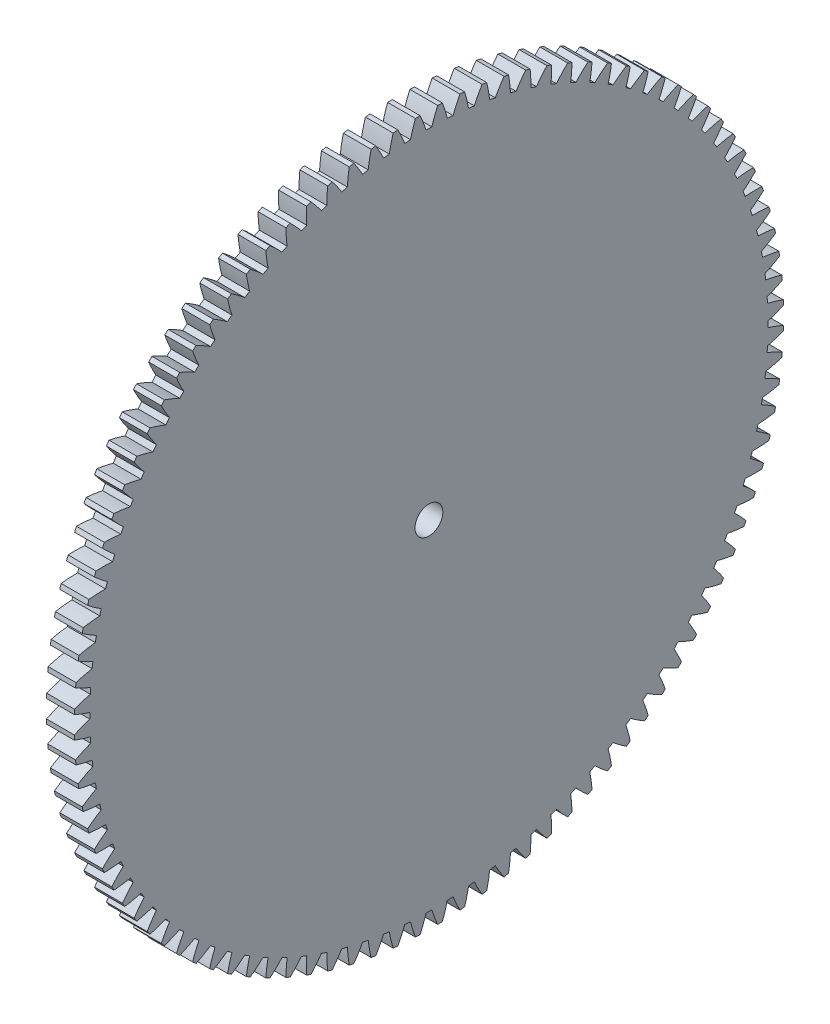
SolidWorks part; units mm, degrees
ref_plane "Plane1" through (0, 0, 0) normal (0, 0, 1) x (1, 0, 0)
ref_plane "Plane2" through (0, 0, 0) normal (0, 1, 0) x (1, 0, 0)
ref_plane "Plane3" through (0, 0, 0) normal (1, 0, 0) x (0, 0, -1)
sketch "HoldingSke" plane through (0, 0, 0) normal (0, 1, 0) x (1, 0, 0)
  line L0 (0, 0) -> (-0.1736, -0.9848)
  line L1 (-15, 0) -> (100, 0) construction
  line L2 (0, 0) -> (-2.1039, 2.3779)
  line L3 (0, 0) -> (-11.863, 4.5341)
  line L4 (0, 0) -> (-1.4996, 8.5048)
  line L5 (0, 0) -> (-46.8476, -17.4728)
  line L6 (0, 0) -> (-3.3159, -2.2372)
  line L7 (-2.1039, 2.3779) -> (8.6586, 51.2059)
  line L8 (-76.2, 54.61) -> (-75.5, 54.61)
  line L9 (-71.009, 38.7566) -> (-53.1078, 45.2721)
  line L10 (-76.2, 71.12) -> (104.1128, 71.12)
  line L11 (0, 0) -> (-4, 0)
  line L12 (-76.2, 101.6) -> (-76.162, 101.6)
  line L13 (24.9733, 27.94) -> (52.9518, 28.4284)
  line L14 (24.9733, 27.94) -> (24.9743, 27.94)
  line L15 (24.9733, 27.94) -> (100.4006, 29.5858)
  line L16 (-63.627, -1) -> (-12.827, -1)
  circle A0 centre (0, 0) radius 2
  circle A1 centre (0, 0) radius 37.5
  circle A2 centre (0, 0) radius 37.5
  circle A3 centre (0, 0) radius 2
  dimension "Hub_dia" = 75
  dimension "Num_teeth" = 100
  dimension "Pitch" = 1
  dimension "Overall_len" = 50
  dimension "Show_teeth" = 100
  dimension "Thickness" = 4
  dimension "OAL" = 50.0001
  dimension "Ap" = 20
  dimension "H" = 19.05
  dimension "Pitch_radius" = 180.3128
  dimension "Width" = 4
  dimension "Backlash" = 0.038
  dimension "Addendum_fac" = 1
  dimension "Dedendum_fac" = 1.25
  dimension "Clearance_fac" = 0.25
  dimension "Dedendum_add" = 0.001
  dimension "Module" = 1
sketch "BasProSke" plane through (0, 0, 0) normal (0, 1, 0) x (1, 0, 0)
  line L0 (-10, 0) -> (60, 0) construction
  line L1 (0, 0) -> (0, 51)
  line L2 (0, 0) -> (4, 0)
  line L3 (4, 0) -> (4, 51)
  line L4 (4, 51) -> (0, 51)
  dimension "Thickness" = 4
revolve "Base-Revolve" add sketch "BasProSke" angle 360 about L0
sketch "TooCutSke" plane through (0, 0, 0) normal (1, 0, 0) x (0, 0, -1)
  line L1 (0, 0) -> (0, 107) construction
  line L2 (0, 0) -> (-0.8519, 49.9927) construction
  line L3 (0, 0) -> (-3.1408, 99.9403) construction
  line L4 (-0.8519, 49.9927) -> (-1.5704, 49.9702) construction
  arc A0 (0.4147, 48.7472) -> (-0.4147, 48.7472) centre (0, 0) ccw
  arc A1 (1.2795, 51.0094) -> (-1.2795, 51.0094) centre (0, 0) ccw
  circle A2 centre (0, 0) radius 50 construction
  circle A3 centre (0, 0) radius 46.9846 construction
  arc A4 (-0.4147, 48.7472) -> (-1.2795, 51.0094) centre (-19.4942, 42.7496) ccw
  arc A5 (1.2795, 51.0094) -> (0.4147, 48.7472) centre (19.4942, 42.7496) ccw
  dimension "Pitch_dia" = 100
  dimension "Base_dia" = 93.9693
  dimension "Flank_rad" = 20
extrude "ToothCut" cut sketch "TooCutSke" along normal through all
fillet "Breaks" [suppressed] radius 0.02
fillet "RootFillets" [suppressed] radius 0.251
pattern_circular "TeethCuts" count 100 every 3.6 about axis through (-10, 0, 0) along (1, 0, 0) of "ToothCut", "RootFillets", "Breaks"
sketch "HubNeaOneSke" plane through (0, 0, 0) normal (-1, 0, 0) x (0, 0, 1)
  circle A0 centre (0, 0) radius 37.5
extrude "HubNearOne" [suppressed] add sketch "HubNeaOneSke" along normal blind 46.0001
sketch "HubNeaBotSke" plane through (0, 0, 0) normal (-1, 0, 0) x (0, 0, 1)
  circle A0 centre (0, 0) radius 37.5
extrude "HubNearBoth" [suppressed] add sketch "HubNeaBotSke" along normal blind 23
ref_plane "FarPln" through (4, 0, 0) normal (1, 0, 0) x (0, 0, -1)
sketch "HubFarSke" plane through (4, 0, 0) normal (1, 0, 0) x (0, 0, -1)
  circle A0 centre (0, 0) radius 37.5
extrude "HubFar" [suppressed] add sketch "HubFarSke" along normal blind 23
sketch "BorSke" plane through (0, 0, 0) normal (1, 0, 0) x (0, 0, -1)
  circle A0 centre (0, 0) radius 2
extrude "Bore" cut sketch "BorSke" along normal mid plane 100.0001
sketch "KeySke" plane through (0, 0, 0) normal (1, 0, 0) x (0, 0, -1)
  line L0 (-0.8, 0) -> (-0.8, 2.7)
  line L1 (-0.8, 2.7) -> (0.8, 2.7)
  line L2 (0.8, 2.7) -> (0.8, 0)
  line L3 (0, 0) -> (0, 34) construction
  line L4 (-0.8, 0) -> (0.8, 0)
extrude "Keyway" [suppressed] cut sketch "KeySke" along normal mid plane 100.0001
pattern_circular "Keyway2" [suppressed] count 2 every 90 about axis through (-10, 0, 0) along (1, 0, 0)
equation "' \"Module@HoldingSke\" = 6.35"
equation "' \"Num_teeth@HoldingSke\" = 12"
equation "' \"Ap@HoldingSke\" =  20"
equation "' \"Ap@HoldingSke\" = 20"
equation "' \"Width@HoldingSke\" = 0.5 * 25.4"
equation "' \"Hub_dia@HoldingSke\"= 1 * 25.4"
equation "' \"Hub_dia@HoldingSke\" = 1 * 25.4"
equation "' \"Overall_len@HoldingSke\" = 1.0 * 25.4"
equation "' \"Bore@HoldingSke\" = 0.75 * 25.4"
equation "' \"T_dim@HoldingSke\" = 0.1 * 25.4"
equation "' \"Width@KeySke\" = 0.25 * 25.4"
equation "' \"Show_teeth@HoldingSke\" = 13"
equation "' \"Backlash@HoldingSke\" = 0.009 * 25.4"
equation "' \"Addendum_fac@HoldingSke\" = 1.0"
equation "' \"Dedendum_fac@HoldingSke\" = 1.25"
equation "' \"Dedendum_add@HoldingSke\" = 0.00005 * 25.4"
equation "' \"Clearance_fac@HoldingSke\" = 0.25"
equation "\"Pitch@HoldingSke\" = 1 / \"Module@HoldingSke\""
equation "\"Overcut_dia@TooCutSke\" = (\"Num_teeth@HoldingSke\" + 2 * \"Addendum_fac@HoldingSke\") / \"Pitch@HoldingSke\" + 0.002 * 25.4"
equation "\"Pitch_dia@TooCutSke\" = \"Num_teeth@HoldingSke\" / \"Pitch@HoldingSke\""
equation "\"Base_dia@TooCutSke\" = \"Num_teeth@HoldingSke\" / \"Pitch@HoldingSke\" * cos((\"Ap@HoldingSke\"  * 3.14159265 / 180))"
equation "\"Root_dia@TooCutSke\" = (\"Num_teeth@HoldingSke\" + 2) / \"Pitch@HoldingSke\" - 2 * (\"Addendum_fac@HoldingSke\" + \"Dedendum_fac@HoldingSke\") / \"Pitch@HoldingSke\" - \"Dedendum_add@HoldingSke\" * 2"
equation "\"Half_ang@TooCutSke\" = 180 / \"Num_teeth@HoldingSke\""
equation "\"Half_CT@TooCutSke\" = \"Num_teeth@HoldingSke\" / \"Pitch@HoldingSke\" * sin((3.14159265 / 2 / \"Num_teeth@HoldingSke\")) / 2 - 7 * \"Backlash@HoldingSke\" / 4"
equation "\"Flank_rad@TooCutSke\" = \"Num_teeth@HoldingSke\" / \"Pitch@HoldingSke\" / 5"
equation "\"Radius@RootFillets\" = \"Clearance_fac@HoldingSke\" / \"Pitch@HoldingSke\" + \"Dedendum_add@HoldingSke\""
equation "\"Break_rad@Breaks\" = 0.02 / \"Pitch@HoldingSke\""
equation "\"Thickness@HoldingSke\" = \"Width@HoldingSke\""
equation "\"OAL@HoldingSke\" = \"Thickness@HoldingSke\""
equation "\"MHD@HoldingSke\" = (\"Num_teeth@HoldingSke\" + 2) / \"Pitch@HoldingSke\" - 2 * (\"Addendum_fac@HoldingSke\" + \"Dedendum_fac@HoldingSke\")  / \"Pitch@HoldingSke\" - \"Dedendum_add@HoldingSke\" * 2"
equation "\"MBD@HoldingSke\" = (\"Num_teeth@HoldingSke\" + 2) / \"Pitch@HoldingSke\" - 2 * (\"Addendum_fac@HoldingSke\" + \"Dedendum_fac@HoldingSke\")  / \"Pitch@HoldingSke\" - \"Dedendum_add@HoldingSke\" * 2 - 0.002 * 25.4"
equation "\"MHD@HoldingSke\" = ((sgn( \"MHD@HoldingSke\" - \"Hub_dia@HoldingSke\" )-1)*( \"MHD@HoldingSke\" - \"Hub_dia@HoldingSke\" ))/-2+ \"Hub_dia@HoldingSke\""
equation "\"MBD@HoldingSke\" = ((sgn( \"MBD@HoldingSke\" - \"Bore@HoldingSke\" )-1)*( \"MBD@HoldingSke\" - \"Bore@HoldingSke\" ))/-2+ \"Bore@HoldingSke\""
equation "\"OAL@HoldingSke\" = ((sgn( \"OAL@HoldingSke\" - \"Overall_len@HoldingSke\" )+1)*( \"OAL@HoldingSke\" - \"Overall_len@HoldingSke\" ))/2 + \"Overall_len@HoldingSke\" + 0.000002 * 25.4"
equation "\"Num_teeth@TeethCuts\" = int( \"Show_teeth@HoldingSke\" ) + 1"
equation "\"Num_teeth@TeethCuts\" = ((sgn( \"Num_teeth@TeethCuts\" - \"Num_teeth@HoldingSke\" )-1)*( \"Num_teeth@TeethCuts\" - \"Num_teeth@HoldingSke\" ))/-2+ \"Num_teeth@HoldingSke\""
equation "\"Num_teeth@TeethCuts\" = ((sgn( \"Num_teeth@TeethCuts\" - 2.0)+1)*( \"Num_teeth@TeethCuts\" - 2.0))/2 +2.0"
equation "\"Angle@TeethCuts\" = 360.0 / \"Num_teeth@HoldingSke\""
equation "\"Diameter@BasProSke\" = (\"Num_teeth@HoldingSke\" + 2 * \"Addendum_fac@HoldingSke\") / \"Pitch@HoldingSke\""
equation "\"Thickness@BasProSke\"  = \"Thickness@HoldingSke\""
equation "' \"Fillet_rad@BasProSke\" =  \"Thickness@HoldingSke\" * 0.05"
equation "' \"Fillet_rad@BasProSke\" = \"Thickness@HoldingSke\" * 0.05"
equation "\"MHD@HoldingSke\" = ((sgn( \"MHD@HoldingSke\" - \"Root_dia@TooCutSke\" )-1)*( \"MHD@HoldingSke\" - \"Root_dia@TooCutSke\" ))/-2+ \"Root_dia@TooCutSke\""
equation "\"Diameter@HubNeaOneSke\" = \"MHD@HoldingSke\""
equation "\"Length@HubNearOne\" = \"OAL@HoldingSke\" - \"Thickness@BasProSke\""
equation "\"Diameter@HubNeaBotSke\" = \"MHD@HoldingSke\""
equation "\"Length@HubNearBoth\" = ( \"OAL@HoldingSke\" - \"Thickness@BasProSke\" ) / 2.0"
equation "\"Thickness@FarPln\" = \"Thickness@BasProSke\""
equation "\"Diameter@HubFarSke\" = \"MHD@HoldingSke\""
equation "\"Length@HubFar\" = ( \"OAL@HoldingSke\" - \"Thickness@BasProSke\" ) / 2.0"
equation "\"Diameter@BorSke\" = \"MBD@HoldingSke\""
equation "\"D1@Bore\" = \"OAL@HoldingSke\" * 2.0"
equation "\"D1@Keyway\" = \"OAL@HoldingSke\" * 2.0"
equation "\"Offset@KeySke\" = \"T_dim@HoldingSke\" + \"MBD@HoldingSke\" / 2.0"
